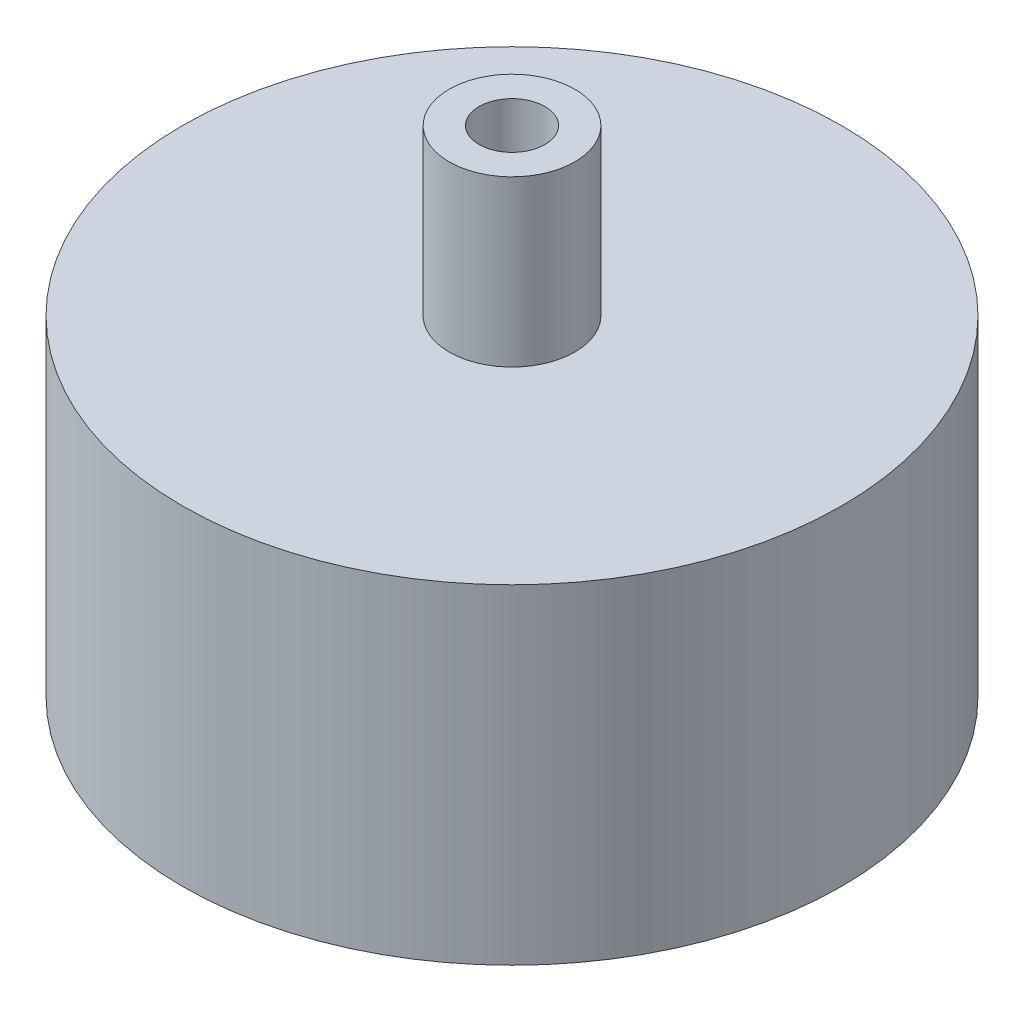
SolidWorks part; units mm, degrees
ref_plane "前视基准面" through (0, 0, 0) normal (0, 0, 1) x (1, 0, 0)
ref_plane "上视基准面" through (0, 0, 0) normal (0, 1, 0) x (1, 0, 0)
ref_plane "右视基准面" through (0, 0, 0) normal (1, 0, 0) x (0, 0, -1)
sketch "草图1" plane through (0, 0, 0) normal (0, 1, 0) x (1, 0, 0)
  circle A0 centre (0, 0) radius 30
  dimension "D1" = 60
extrude "凸台-拉伸1" add sketch "草图1" along normal blind 30
sketch "草图2" plane through (0, 30, 0) normal (0, 1, 0) x (1, 0, 0)
  circle A0 centre (0, 0) radius 5.725
  circle A1 centre (0, 0) radius 3
  dimension "D1" = 11.45
  dimension "D2" = 6
extrude "凸台-拉伸2" add sketch "草图2" along normal blind 15
